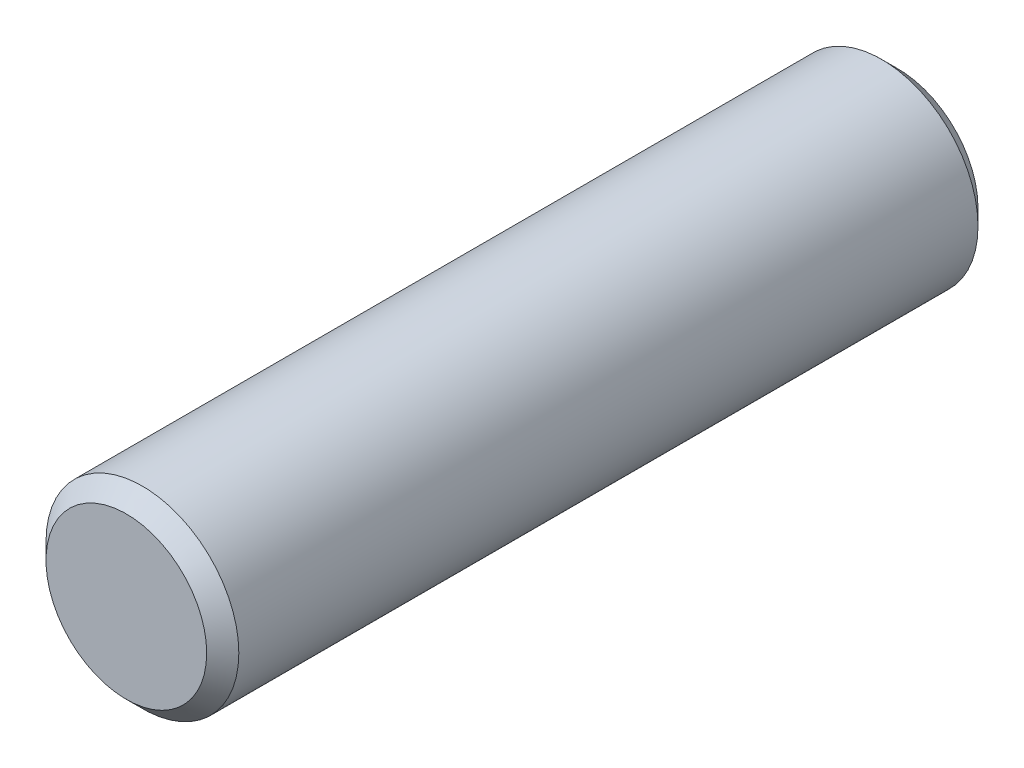
SolidWorks part; units mm, degrees
ref_plane "Plan1" through (0, 0, 0) normal (0, 0, 1) x (1, 0, 0)
ref_plane "Plan2" through (0, 0, 0) normal (0, 1, 0) x (1, 0, 0)
ref_plane "Plan3" through (0, 0, 0) normal (1, 0, 0) x (0, 0, -1)
sketch "Esquisse1" plane through (0, 0, 0) normal (0, 0, 1) x (1, 0, 0)
  circle A0 centre (0, 0) radius 3
  dimension "D1" = 6
extrude "Base-Extrusion" add sketch "Esquisse1" along normal blind 24
chamfer "Chanfrein1" distance 0.5 angle 45
